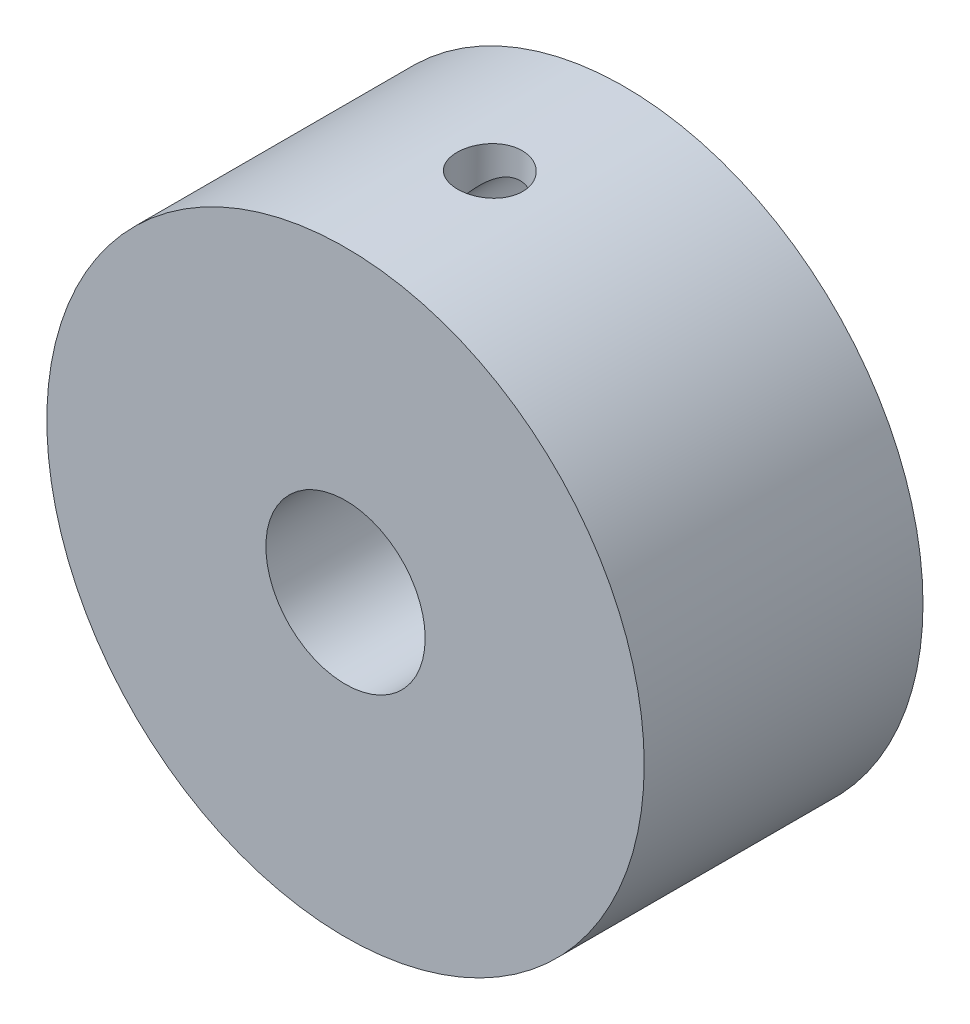
SolidWorks part; units mm, degrees
ref_plane "Front Plane" through (0, 0, 0) normal (0, 0, 1) x (1, 0, 0)
ref_plane "Top Plane" through (0, 0, 0) normal (0, 1, 0) x (1, 0, 0)
ref_plane "Right Plane" through (0, 0, 0) normal (1, 0, 0) x (0, 0, -1)
sketch "Sketch1" plane through (0, 0, 0) normal (0, 0, 1) x (1, 0, 0)
  circle A0 centre (0, 0) radius 15
  circle A1 centre (0, 0) radius 4
  point P4 (0, 0)
  dimension "D1" = 30
  dimension "D2" = 8
extrude "Boss-Extrude1" add sketch "Sketch1" along normal blind 14
hole_wizard "M4x0.7 Tapped Hole1" positions "3DSketch1" profile "Sketch2" tap size "M4x0.7" standard "ANSI Metric"
sketch3d "3DSketch1"
  point P0 (0.2468, 14.998, 7)
  point P3 (0, 0, 0)
  point P7 (0, 0, 0)
  dimension "D1" = 7
sketch "Sketch2" plane through (0.2468, 14.998, 7) normal (0, 0, 1) x (-0.9999, 0.0165, 0)
  line L0 (0, 0) -> (0, 11)
  line L1 (0, 11) -> (1.65, 11)
  line L2 (1.65, 11) -> (1.65, 0)
  line L5 (1.65, 0) -> (0, 0)
  line L11 (0, -6.35) -> (0, 107.95) construction
  dimension "Thru Tap Drill Dia." = 3.3
  dimension "Thru Tap Drill Depth" = 11
cosmetic thread "Hole Thread1"
sketch "Sketch3" plane through (0, 0, 0) normal (0, 0, -1) x (-1, 0, 0)
sketch "Sketch6" plane through (0, 0, 0) normal (0, 0, -1) x (-1, 0, 0)
  circle A0 centre (0, 0) radius 12
hole_wizard "M4x0.7 Tapped Hole3" positions "Sketch7" profile "Sketch8" tap size "M4x0.7" standard "ANSI Metric"
sketch "Sketch7" plane through (0, 0, 0) normal (0, 0, -1) x (-1, 0, 0)
  circle A0 centre (0, 0) radius 12 construction
  point P0 (0, 12)
  point P4 (-12, 0)
  point P6 (0, -12)
  point P8 (12, 0)
sketch "Sketch8" plane through (0, 12, 0) normal (1, 0, 0) x (0, 1, 0)
  line L0 (0, 0) -> (0, 8.9914)
  line L1 (0, 8.9914) -> (1.65, 8)
  line L2 (1.65, 8) -> (1.65, 0)
  line L5 (1.65, 0) -> (0, 0)
  line L10 (0, 8.9914) -> (-1.65, 8) construction
  line L11 (0, -6.35) -> (0, 107.95) construction
  dimension "Tap Drill Dia." = 3.3
  dimension "Tap Drill Depth" = 8
  dimension "Drill Angle" = 118
cosmetic thread "Hole Thread6"
cosmetic thread "Hole Thread7"
cosmetic thread "Hole Thread8"
cosmetic thread "Hole Thread9"
